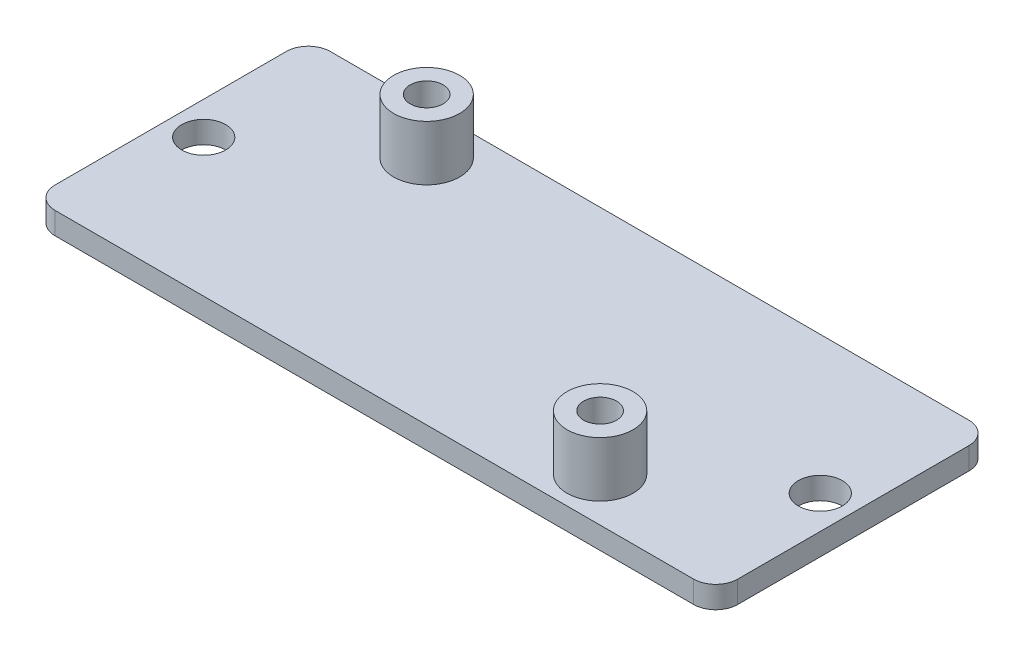
SolidWorks part; units mm, degrees
material "ABS"
ref_plane "Спереди" through (0, 0, 0) normal (0, 0, 1) x (1, 0, 0)
ref_plane "Сверху" through (0, 0, 0) normal (0, 1, 0) x (1, 0, 0)
ref_plane "Справа" through (0, 0, 0) normal (1, 0, 0) x (0, 0, -1)
sketch "Эскиз1" plane through (0, 0, 0) normal (0, 1, 0) x (1, 0, 0)
  line L1 (0, 0) -> (62, 0)
  line L2 (0, 0) -> (0, -25)
  line L3 (0, -25) -> (62, -25)
  line L4 (62, 0) -> (62, -25)
  dimension "D1" = 25
  dimension "D2" = 62
extrude "Бобышка-Вытянуть1" add sketch "Эскиз1" along normal blind 2
sketch "Эскиз2" plane through (0, 2, 0) normal (0, 1, 0) x (1, 0, 0)
  line L0 (0, 0) -> (0, -25) construction
  line L1 (62, -25) -> (62, 0) construction
  line L2 (62, 0) -> (0, 0) construction
  line L3 (0, -25) -> (62, -25) construction
  circle A0 centre (14.75, -4) radius 3
  circle A1 centre (47.5, -21) radius 3
  dimension "D2" = 14.5
  dimension "D4" = 4
  dimension "D5" = 6
  dimension "D6" = 6
  dimension "D1" = 14.75
  dimension "D3" = 4
extrude "Бобышка-Вытянуть2" add sketch "Эскиз2" along normal blind 5
sketch "Эскиз3" plane through (0, 7, 0) normal (0, 1, 0) x (1, 0, 0)
  circle A0 centre (14.75, -4) radius 1.5
  circle A1 centre (47.5, -21) radius 1.5
  dimension "D1" = 3
  dimension "D2" = 3
extrude "Вырез-Вытянуть1" cut sketch "Эскиз3" against normal through all both and the other way through all
sketch "Эскиз4" plane through (0, 2, 0) normal (0, 1, 0) x (1, 0, 0)
  line L0 (0, -12.5) -> (62, -12.5) construction
  line L1 (0, 0) -> (0, -25) construction
  line L2 (62, -25) -> (62, 0) construction
  circle A0 centre (3, -12.5) radius 2
  circle A1 centre (59, -12.5) radius 2
  dimension "D1" = 4
  dimension "D2" = 4
  dimension "D3" = 3
  dimension "D4" = 3
extrude "Вырез-Вытянуть2" cut sketch "Эскиз4" against normal through all both and the other way through all
fillet "Скругление1" radius 2 1 edges at (0, 1, 0)
fillet "Скругление2" radius 2 1 edges at (0, 1, 25)
fillet "Скругление3" radius 2 1 edges at (62, 1, 25)
fillet "Скругление4" radius 2 1 edges at (62, 1, 0)
